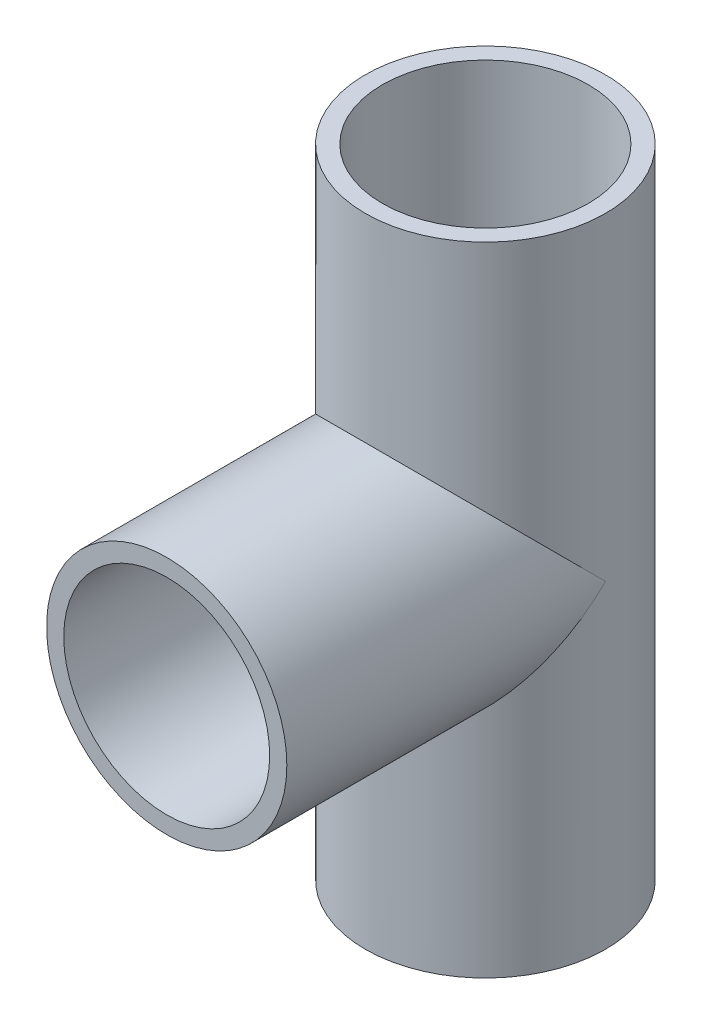
SolidWorks part; units mm, degrees
ref_plane "Front Plane" through (0, 0, 0) normal (0, 0, 1) x (1, 0, 0)
ref_plane "Top Plane" through (0, 0, 0) normal (0, 1, 0) x (1, 0, 0)
ref_plane "Right Plane" through (0, 0, 0) normal (1, 0, 0) x (0, 0, -1)
sketch "Sketch1" plane through (0, 0, 0) normal (0, 1, 0) x (1, 0, 0)
  circle A0 centre (0, 0) radius 24.5
  circle A1 centre (0, 0) radius 21
  dimension "D1" = 49
  dimension "D2" = 42
extrude "Boss-Extrude1" add sketch "Sketch1" along normal blind 130
sketch "Sketch3" plane through (0, 0, 0) normal (0, 0, 1) x (1, 0, 0)
  circle A0 centre (0, 65) radius 24.5
  circle A1 centre (0, 65) radius 21
  dimension "D1" = 42
extrude "Boss-Extrude2" add sketch "Sketch3" along normal blind 65
